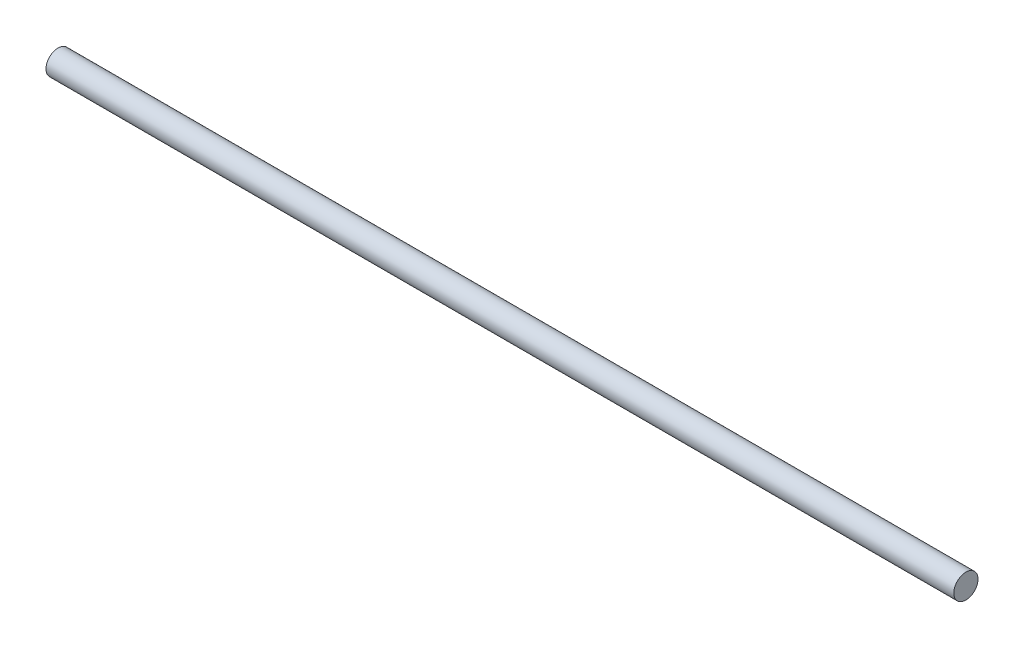
SolidWorks part; units mm, degrees
ref_plane "Front Plane" through (0, 0, 0) normal (0, 0, 1) x (1, 0, 0)
ref_plane "Top Plane" through (0, 0, 0) normal (0, 1, 0) x (1, 0, 0)
ref_plane "Right Plane" through (0, 0, 0) normal (1, 0, 0) x (0, 0, -1)
sketch "Sketch1" plane through (0, 0, 0) normal (1, 0, 0) x (0, 0, -1)
  circle A0 centre (0, 0) radius 4
extrude "Boss-Extrude1" add sketch "Sketch1" along normal blind 300
